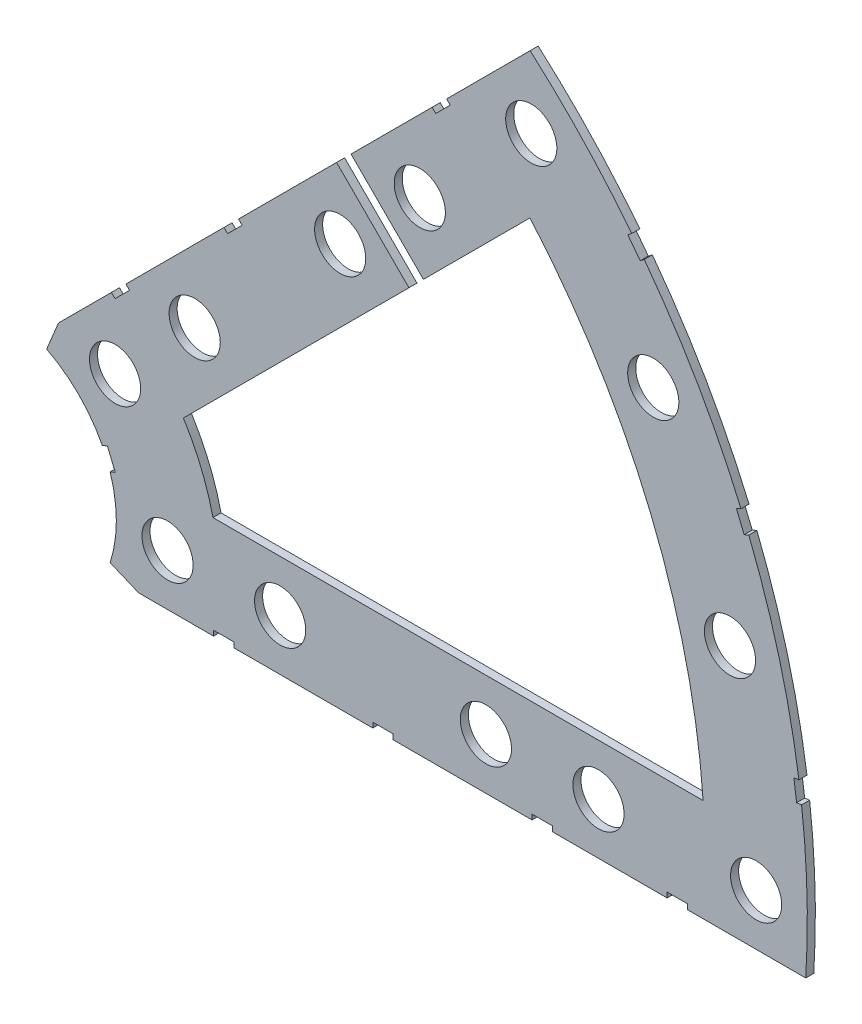
SolidWorks part; units mm, degrees
material "Copper"
ref_plane "Front Plane" through (0, 0, 0) normal (0, 0, 1) x (1, 0, 0)
ref_plane "Top Plane" through (0, 0, 0) normal (0, 1, 0) x (1, 0, 0)
ref_plane "Right Plane" through (0, 0, 0) normal (1, 0, 0) x (0, 0, -1)
sketch "Sketch1" plane through (0, 0, 0) normal (0, 0, 1) x (1, 0, 0)
  line L0 (0, 0) -> (320.3893, 0) construction
  line L1 (0, 0) -> (155.5285, 155.5285) construction
  line L2 (67.2115, 76.1917) -> (8.6967, 17.6769)
  line L3 (8.6967, 17.6769) -> (7.229, 14.1336)
  line L4 (101.4014, -6.35) -> (18.6489, -6.35)
  line L5 (15.1056, -4.8823) -> (18.6489, -6.35)
  line L6 (88.6729, 6.35) -> (27.8605, 6.35)
  line L9 (67.1914, 58.2111) -> (24.1905, 15.2102)
  line L10 (0, 0) -> (40.4486, 97.6516) construction
  line L11 (0, 0) -> (123.4567, -51.1374) construction
  line L18 (8.6967, 17.6769) -> (13.294, 8.6183) construction
  line L19 (18.6489, -6.35) -> (15.4943, 3.3063) construction
  line L20 (27.8605, 6.35) -> (27.7442, 6.7059) construction
  line L21 (24.1905, 15.2102) -> (24.3599, 14.8764) construction
  arc A0 (7.229, 14.1336) -> (15.1056, -4.8823) centre (0, 0) cw
  arc A1 (67.2115, 76.1917) -> (101.4014, -6.35) centre (0, 0) cw
  arc A2 (24.1905, 15.2102) -> (27.8605, 6.35) centre (0, 0) cw
  arc A3 (67.1914, 58.2111) -> (88.6729, 6.35) centre (0, 0) cw
  arc A8 (13.294, 8.6183) -> (15.4943, 3.3063) centre (0, 0) cw construction
  arc A9 (24.3599, 14.8764) -> (27.7442, 6.7059) centre (0, 0) cw construction
  dimension "D1" = 45
  dimension "D3" = 6.35
  dimension "D4" = 15.875
  dimension "D7" = 22.5
  dimension "D8" = 101.6
  dimension "D11" = 12.7
  dimension "D12" = 12.7
  dimension "D2" = 6.35
  dimension "D5" = 67.5
  dimension "D9" = 1.27
  dimension "D10" = 1.27
  dimension "D6" = 12.7
extrude "Boss-Extrude1" add sketch "Sketch1" along normal blind 1
sketch "Sketch2" plane through (0, 0, 1) normal (0, 0, 1) x (1, 0, 0)
  line L0 (0, 0) -> (101.6, 0) construction
  line L1 (0, 0) -> (71.842, 71.842) construction
  line L3 (0, 0) -> (22.225, 0) construction
  line L4 (0, 0) -> (15.7154, 15.7154) construction
  line L5 (0, 0) -> (95.25, 0) construction
  line L6 (0, 0) -> (92.0044, 24.6525) construction
  arc A0 (101.4014, -6.35) -> (67.2115, 76.1917) centre (0, 0) ccw construction
  circle A1 centre (22.225, 0) radius 3.175
  arc A2 (15.1056, -4.8823) -> (7.229, 14.1336) centre (0, 0) ccw construction
  circle A3 centre (36.195, 0) radius 3.175
  circle A4 centre (61.722, 0) radius 3.175
  circle A5 centre (75.692, 0) radius 3.175
  circle A6 centre (95.25, 0) radius 3.175
  circle A7 centre (15.7154, 15.7154) radius 3.175
  circle A8 centre (25.5937, 25.5937) radius 3.175
  circle A9 centre (43.644, 43.644) radius 3.175
  circle A10 centre (53.5223, 53.5223) radius 3.175
  circle A11 centre (92.0044, 24.6525) radius 3.175
  circle A12 centre (82.4889, 47.625) radius 3.175
  circle A13 centre (67.3519, 67.3519) radius 3.175
  dimension "D3" = 6.35
  dimension "D1" = 45
  dimension "D2" = 6.35
  dimension "D4" = 6.35
  dimension "D5" = 13.97
  dimension "D7" = 13.97
  dimension "D8" = 19.558
  dimension "D9" = 45
  dimension "D10" = 15
  dimension "D11" = 25.527
  dimension "D6" = 2
extrude "Cut-Extrude1" cut sketch "Sketch2" against normal through all
sketch "Sketch3" plane through (0, 0, 1) normal (0, 0, 1) x (1, 0, 0)
  line L0 (15.2664, 24.2467) -> (17.0625, 26.0427)
  line L1 (15.2664, 24.2467) -> (15.7154, 23.7977)
  line L2 (17.0625, 26.0427) -> (17.5115, 25.5937)
  line L3 (15.7154, 23.7977) -> (17.5115, 25.5937)
  line L4 (67.2115, 76.1917) -> (8.6967, 17.6769) construction
  line L5 (43.195, 52.1753) -> (44.9911, 53.9713)
  line L6 (43.195, 52.1753) -> (52.1753, 43.195)
  line L7 (44.9911, 53.9713) -> (53.9713, 44.9911)
  line L8 (52.1753, 43.195) -> (53.9713, 44.9911)
  line L9 (27.94, -6.35) -> (30.48, -6.35)
  line L10 (27.94, -6.35) -> (27.94, -5.715)
  line L11 (30.48, -6.35) -> (30.48, -5.715)
  line L12 (27.94, -5.715) -> (30.48, -5.715)
  line L13 (18.6489, -6.35) -> (101.4014, -6.35) construction
  line L14 (67.437, -6.35) -> (69.977, -6.35)
  line L15 (67.437, -6.35) -> (67.437, -5.715)
  line L16 (69.977, -6.35) -> (69.977, -5.715)
  line L17 (67.437, -5.715) -> (69.977, -5.715)
  line L18 (29.2307, 38.211) -> (31.0268, 40.007)
  line L19 (29.2307, 38.211) -> (29.6797, 37.762)
  line L20 (31.0268, 40.007) -> (31.4758, 39.558)
  line L21 (29.6797, 37.762) -> (31.4758, 39.558)
  line L22 (56.845, 65.8253) -> (55.049, 64.0292)
  line L23 (56.845, 65.8253) -> (57.294, 65.3763)
  line L24 (55.049, 64.0292) -> (55.498, 63.5802)
  line L25 (57.294, 65.3763) -> (55.498, 63.5802)
  line L26 (47.6885, -6.35) -> (50.2285, -6.35)
  line L27 (47.6885, -6.35) -> (47.6885, -5.715)
  line L28 (50.2285, -6.35) -> (50.2285, -5.715)
  line L29 (47.6885, -5.715) -> (50.2285, -5.715)
  line L30 (84.201, -6.35) -> (86.741, -6.35)
  line L31 (84.201, -6.35) -> (84.201, -5.715)
  line L32 (86.741, -6.35) -> (86.741, -5.715)
  line L33 (84.201, -5.715) -> (86.741, -5.715)
  line L34 (0, 0) -> (100.7308, 13.2615) construction
  line L35 (0, 0) -> (93.8662, 38.8806) construction
  line L36 (0, 0) -> (80.6047, 61.8502) construction
  line L37 (0, 0) -> (101.6, 0) construction
  line L38 (99.9355, 14.4377) -> (100.267, 11.9194)
  line L39 (99.9355, 14.4377) -> (101.1946, 14.6035)
  line L40 (100.267, 11.9194) -> (101.5261, 12.0852)
  line L41 (101.1946, 14.6035) -> (101.5261, 12.0852)
  line L42 (99.9355, 14.4377) -> (101.5261, 12.0852) construction
  line L43 (100.267, 11.9194) -> (101.1946, 14.6035) construction
  line L44 (93.7655, 37.4643) -> (94.9388, 37.9503)
  line L45 (93.7655, 37.4643) -> (92.7935, 39.811)
  line L46 (94.9388, 37.9503) -> (93.9668, 40.297)
  line L47 (92.7935, 39.811) -> (93.9668, 40.297)
  line L48 (93.7655, 37.4643) -> (93.9668, 40.297) construction
  line L49 (94.9388, 37.9503) -> (92.7935, 39.811) construction
  line L50 (79.3278, 62.4712) -> (80.874, 60.456)
  line L51 (79.3278, 62.4712) -> (80.3354, 63.2443)
  line L52 (80.874, 60.456) -> (81.8816, 61.2292)
  line L53 (80.3354, 63.2443) -> (81.8816, 61.2292)
  line L54 (79.3278, 62.4712) -> (81.8816, 61.2292) construction
  line L55 (80.874, 60.456) -> (80.3354, 63.2443) construction
  line L56 (13.5939, 7.0054) -> (14.5659, 4.6588)
  line L57 (13.5939, 7.0054) -> (14.7672, 7.4914)
  line L58 (14.5659, 4.6588) -> (15.7393, 5.1448)
  line L59 (14.7672, 7.4914) -> (15.7393, 5.1448)
  line L60 (13.5939, 7.0054) -> (15.7393, 5.1448) construction
  line L61 (14.5659, 4.6588) -> (14.7672, 7.4914) construction
  circle A0 centre (15.7154, 15.7154) radius 3.175 construction
  circle A1 centre (25.5937, 25.5937) radius 3.175 construction
  circle A2 centre (22.225, 0) radius 3.175 construction
  circle A3 centre (61.722, 0) radius 3.175 construction
  arc A4 (101.4014, -6.35) -> (67.2115, 76.1917) centre (0, 0) ccw construction
  arc A9 (15.1056, -4.8823) -> (7.229, 14.1336) centre (0, 0) ccw construction
  circle A10 centre (43.644, 43.644) radius 3.175 construction
  circle A11 centre (53.5223, 53.5223) radius 3.175 construction
  circle A12 centre (36.195, 0) radius 3.175 construction
  circle A13 centre (75.692, 0) radius 3.175 construction
  point P75 (14.6666, 6.0751)
  dimension "D2" = 5.715
  dimension "D3" = 2.54
  dimension "D8" = 0.635
  dimension "D9" = 5.715
  dimension "D12" = 5.715
  dimension "D4" = 7.5
  dimension "D5" = 22.5
  dimension "D7" = 37.5
  dimension "D10" = 90
  dimension "D11" = 1.27
  dimension "D14" = 0.635
  dimension "D15" = 90
  dimension "D18" = 0.635
  dimension "D19" = 90
  dimension "D22" = 0.635
  dimension "D20" = 1.27
  dimension "D17" = 0.635
  dimension "D6" = 12.7
  dimension "D21" = 2.54
  dimension "D25" = 5.715
  dimension "D13" = 11.4935
  dimension "D16" = 8.509
  dimension "D23" = 11.4935
  dimension "D24" = 8.509
extrude "Cut-Extrude2" cut sketch "Sketch3" against normal through all
equation "\"cSep\"= 1.005"
equation "\"D11@Sketch2\"=\"cSep\""
equation "\"cSep2\"= \"D8@Sketch2\""
equation "\"D13@Sketch3\"=\"cSep\"/2-.05"
equation "\"D16@Sketch3\"=\"cSep2\"/2-.05"
equation "\"D23@Sketch3\"=\"cSep\"/2-.05"
equation "\"D24@Sketch3\"=\"cSep2\"/2-.05"
